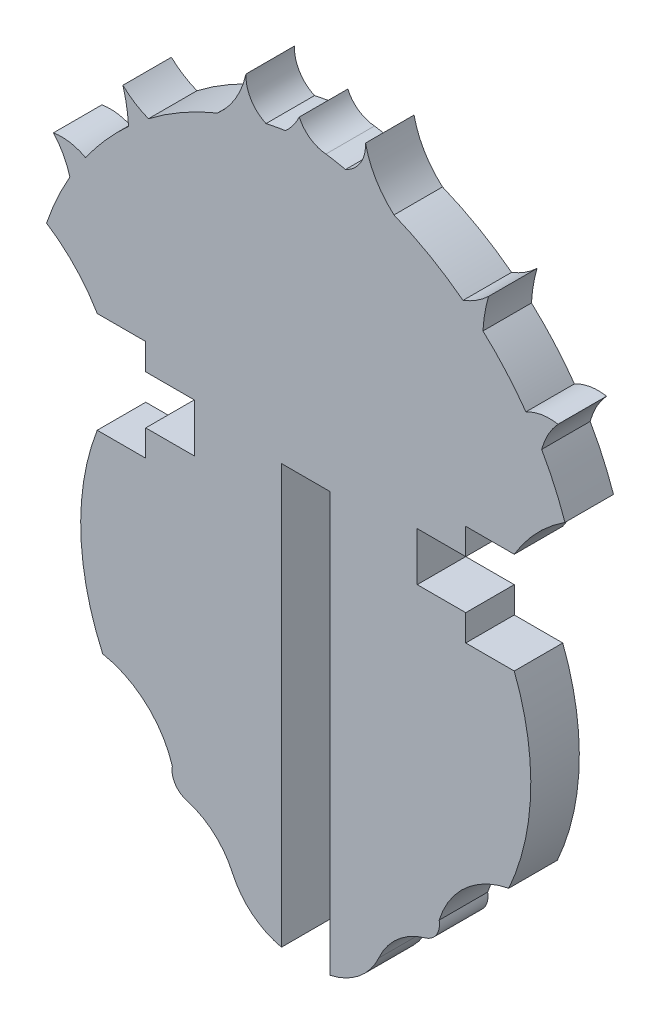
SolidWorks part; units mm, degrees
ref_plane "Front Plane" through (0, 0, 0) normal (0, 0, 1) x (1, 0, 0)
ref_plane "Top Plane" through (0, 0, 0) normal (0, 1, 0) x (1, 0, 0)
ref_plane "Right Plane" through (0, 0, 0) normal (1, 0, 0) x (0, 0, -1)
sketch "Sketch1" plane through (0, 0, 0) normal (0, 0, 1) x (1, 0, 0)
  line L0 (22.4392, 2.2811) -> (22.4392, 15.4404)
  line L1 (22.4392, 15.4404) -> (23.9632, 15.4404)
  line L2 (23.9632, 15.4404) -> (23.9632, 2.2811)
  line L3 (29.7516, 13.452) -> (28.2276, 13.452)
  line L4 (28.2276, 13.452) -> (28.2276, 14.2775)
  line L5 (28.2276, 16.627) -> (29.7516, 16.627)
  line L6 (19.6988, 15.8015) -> (19.6988, 14.2775)
  line L7 (18.1748, 15.8015) -> (18.1748, 16.627)
  line L8 (28.2276, 15.8015) -> (26.7036, 15.8015)
  line L9 (28.2276, 14.2775) -> (26.7036, 14.2775)
  line L10 (28.2276, 15.8015) -> (28.2276, 16.627)
  line L11 (26.7036, 15.8015) -> (26.7036, 14.2775)
  line L12 (18.1748, 14.2775) -> (19.6988, 14.2775)
  line L13 (18.1748, 15.8015) -> (19.6988, 15.8015)
  line L14 (18.1748, 16.627) -> (16.6508, 16.627)
  line L15 (18.1748, 13.452) -> (18.1748, 14.2775)
  line L16 (16.6508, 13.452) -> (18.1748, 13.452)
  arc A0 (23.9632, 2.2811) -> (25.4968, 3.5179) centre (23.4932, 4.4331) ccw
  arc A1 (25.4968, 3.5179) -> (26.9443, 4.7906) centre (27.5853, 2.6021) cw
  arc A2 (26.9443, 4.7906) -> (27.3918, 5.4938) centre (26.7914, 5.3819) ccw
  arc A3 (27.3918, 5.4938) -> (29.5792, 7.4541) centre (30.1176, 4.6528) cw
  arc A4 (29.5792, 7.4541) -> (29.7516, 13.452) centre (22.5045, 10.6588) ccw
  arc A5 (29.7516, 16.627) -> (31.3446, 18.291) centre (34.0626, 14.0944) cw
  arc A6 (31.3446, 18.291) -> (30.6119, 19.91) centre (22.4144, 15.2253) ccw
  arc A7 (30.6119, 19.91) -> (31.1278, 20.8549) centre (32.7952, 19.3312) cw
  arc A8 (31.1278, 20.8549) -> (30.1176, 20.6848) centre (30.8693, 19.3057) ccw
  arc A9 (28.7676, 22.2097) -> (28.9451, 23.2411) centre (33.214, 21.9753) cw
  arc A10 (28.9451, 23.2411) -> (28.1429, 22.7306) centre (27.2343, 25.0443) cw
  arc A11 (25.9737, 23.9704) -> (25.0791, 25.4793) centre (27.8003, 26.0729) cw
  arc A12 (25.0791, 25.4793) -> (24.4505, 24.4448) centre (23.9991, 25.4274) cw
  arc A13 (24.4505, 24.4448) -> (23.8361, 24.5593) centre (22.4144, 15.2253) ccw
  arc A14 (28.1429, 22.7306) -> (25.9737, 23.9704) centre (22.4144, 15.2253) ccw
  arc A15 (30.1176, 20.6848) -> (28.7676, 22.2097) centre (22.4144, 15.2253) ccw
  arc A16 (16.2847, 20.6848) -> (17.6348, 22.2097) centre (23.988, 15.2253) cw
  arc A17 (18.2595, 22.7306) -> (20.4287, 23.9704) centre (23.988, 15.2253) cw
  arc A18 (21.9518, 24.4448) -> (22.5662, 24.5593) centre (23.988, 15.2253) cw
  arc A19 (21.3232, 25.4793) -> (21.9518, 24.4448) centre (22.4033, 25.4274) ccw
  arc A20 (20.4287, 23.9704) -> (21.3232, 25.4793) centre (18.602, 26.0729) ccw
  arc A21 (17.4572, 23.2411) -> (18.2595, 22.7306) centre (19.1681, 25.0443) ccw
  arc A22 (17.6348, 22.2097) -> (17.4572, 23.2411) centre (13.1884, 21.9753) ccw
  arc A23 (15.2745, 20.8549) -> (16.2847, 20.6848) centre (15.5331, 19.3057) cw
  arc A24 (15.7905, 19.91) -> (15.2745, 20.8549) centre (13.6072, 19.3312) ccw
  arc A25 (15.0578, 18.291) -> (15.7905, 19.91) centre (23.988, 15.2253) cw
  arc A26 (16.6508, 16.627) -> (15.0578, 18.291) centre (12.3398, 14.0944) ccw
  arc A27 (16.8231, 7.4541) -> (16.6508, 13.452) centre (23.8978, 10.6588) cw
  arc A28 (19.0106, 5.4938) -> (16.8231, 7.4541) centre (16.2847, 4.6528) ccw
  arc A29 (19.4581, 4.7906) -> (19.0106, 5.4938) centre (19.611, 5.3819) cw
  arc A30 (20.9056, 3.5179) -> (19.4581, 4.7906) centre (18.8171, 2.6021) ccw
  arc A31 (22.4392, 2.2811) -> (20.9056, 3.5179) centre (22.9092, 4.4331) cw
  arc A32 (22.5662, 24.5593) -> (22.9986, 25.1469) centre (21.2669, 25.9681) ccw
  arc A33 (22.9986, 25.1469) -> (23.8361, 24.5593) centre (23.9078, 25.5522) ccw
extrude "Boss-Extrude2" add sketch "Sketch1" along normal blind 1.524
